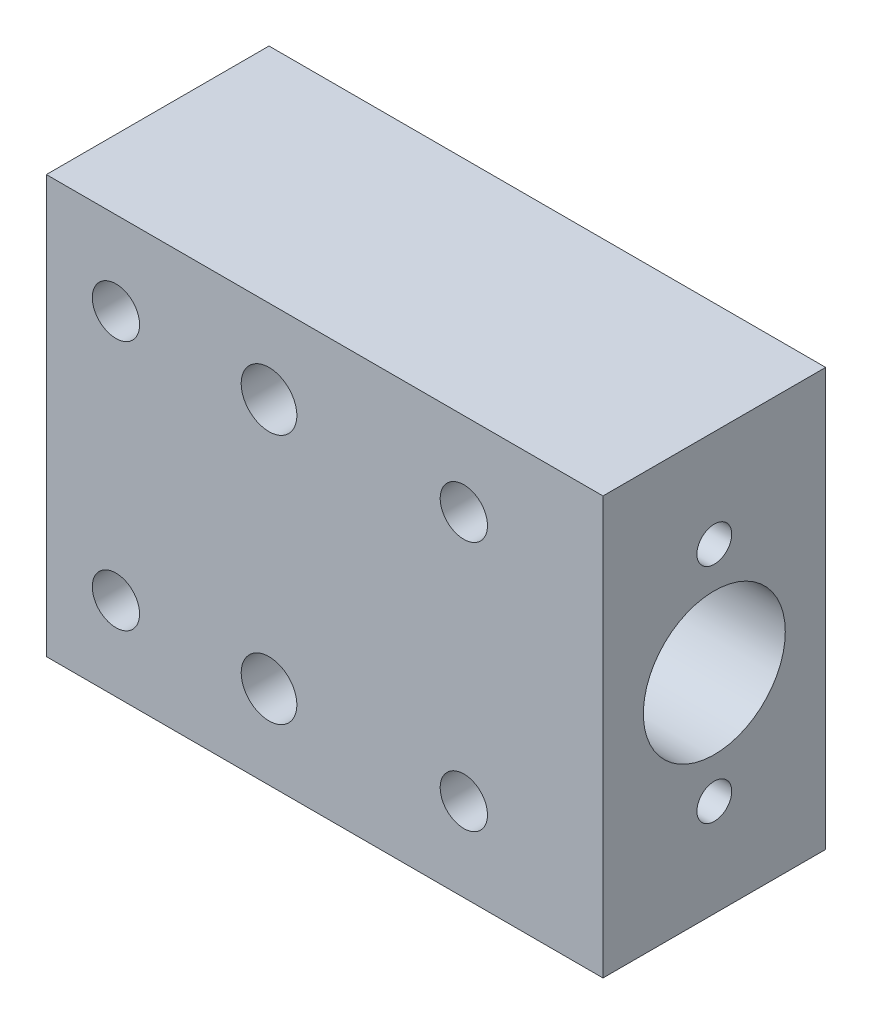
SolidWorks part; units mm, degrees
ref_plane "Alzado" through (0, 0, 0) normal (0, 0, 1) x (1, 0, 0)
ref_plane "Planta" through (0, 0, 0) normal (0, 1, 0) x (1, 0, 0)
ref_plane "Vista lateral" through (0, 0, 0) normal (1, 0, 0) x (0, 0, -1)
sketch "Croquis1" plane through (0, 0, 0) normal (0, 0, 1) x (1, 0, 0)
  line L1 (0, 0) -> (40, 0)
  line L2 (0, 0) -> (0, 30)
  line L3 (0, 30) -> (40, 30)
  line L4 (40, 0) -> (40, 30)
  dimension "D1" = 30
  dimension "D2" = 40
extrude "Saliente-Extruir1" add sketch "Croquis1" along normal blind 16
sketch "Croquis2" plane through (40, 0, 0) normal (1, 0, 0) x (0, 0, -1)
  line L0 (0, 0) -> (0, 30) construction
  line L1 (-16, 0) -> (0, 0) construction
  circle A0 centre (-8, 15) radius 5.1
  dimension "D1" = 10.2
  dimension "D2" = 8
  dimension "D3" = 15
extrude "Cortar-Extruir1" cut sketch "Croquis2" against normal through all
hole_wizard "Refrentado para tornillo con cabeza hueca de M31" positions "Croquis3" profile "Croquis4" counterbore size "M3" standard "DIN" end condition through all
sketch "Croquis3" plane through (0, 0, 0) normal (0, 0, -1) x (-1, 0, 0)
  line L0 (0, 0) -> (-40, 0) construction
  line L1 (-40, 0) -> (-40, 30) construction
  line L2 (0, 30) -> (0, 0) construction
  line L3 (-40, 30) -> (0, 30) construction
  point P0 (-5, 6)
  point P2 (-30, 6)
  point P4 (-30, 24)
  point P6 (-5, 24)
  dimension "D1" = 6
  dimension "D2" = 10
  dimension "D3" = 5
  dimension "D4" = 6
  dimension "D5" = 6
  dimension "D6" = 10
  dimension "D7" = 5
  dimension "D8" = 6
sketch "Croquis4" plane through (5, 6, 0) normal (1, 0, 0) x (0, 1, 0)
  line L0 (0, 0) -> (0, 16)
  line L1 (0, 16) -> (1.7, 16)
  line L3 (1.7, 16) -> (1.7, 3.4)
  line L4 (1.7, 3.4) -> (3.25, 3.4)
  line L5 (3.25, 3.4) -> (3.25, 0)
  line L7 (3.25, 0) -> (0, 0)
  line L11 (0, -6.35) -> (0, 107.95) construction
  dimension "Diámetro de taladro hasta el siguiente" = 3.4
  dimension "Profundidad de taladro hasta el siguiente" = 16
  dimension "Diámetro de refrentado" = 6.5
  dimension "Profundidad de refrentado" = 3.4
hole_wizard "Diámetro de taladro Ø4.0 (4)1" positions "Croquis5" profile "Croquis6" hole size "Ø4.0" standard "DIN" end condition through all
sketch "Croquis5" plane through (0, 0, 0) normal (0, 0, -1) x (-1, 0, 0)
  line L0 (0, 0) -> (-40, 0) construction
  line L1 (-40, 0) -> (-40, 30) construction
  line L2 (-40, 30) -> (0, 30) construction
  point P0 (-16, 6)
  point P2 (-16, 24)
  dimension "D1" = 6
  dimension "D2" = 24
  dimension "D3" = 6
  dimension "D4" = 24
sketch "Croquis6" plane through (16, 6, 0) normal (1, 0, 0) x (0, 1, 0)
  line L0 (0, 0) -> (0, 16)
  line L1 (0, 16) -> (2, 16)
  line L2 (2, 16) -> (2, 0)
  line L5 (2, 0) -> (0, 0)
  line L11 (0, -6.35) -> (0, 107.95) construction
  dimension "Diámetro de taladro hasta el siguiente" = 4
  dimension "Profundidad de taladro hasta el siguiente" = 16
sketch "Croquis7" plane through (40, 0, 0) normal (1, 0, 0) x (0, 0, -1)
  line L0 (-8, 30) -> (-8, 0) construction
  line L1 (-16, 30) -> (0, 30) construction
  line L2 (-16, 0) -> (0, 0) construction
  circle A0 centre (-8, 23) radius 1.25
  circle A1 centre (-8, 7) radius 1.25
  circle A2 centre (-8, 15) radius 8 construction
  dimension "D1" = 16
  dimension "D2" = 2.5
  dimension "D3" = 2.5
extrude "Cortar-Extruir2" cut sketch "Croquis7" against normal blind 7
